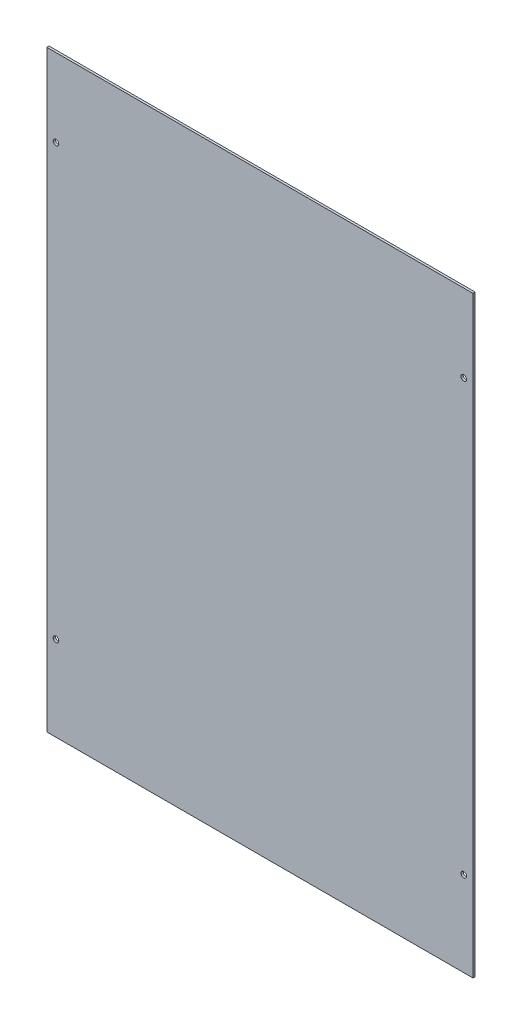
SolidWorks part; units mm, degrees
material "Acrylic (Medium-high impact)"
ref_plane "Front Plane" through (0, 0, 0) normal (0, 0, 1) x (1, 0, 0)
ref_plane "Top Plane" through (0, 0, 0) normal (0, 1, 0) x (1, 0, 0)
ref_plane "Right Plane" through (0, 0, 0) normal (1, 0, 0) x (0, 0, -1)
sketch "Sketch1" plane through (0, 0, 0) normal (0, 0, 1) x (1, 0, 0)
  line L1 (292.1, -406.4) -> (-292.1, -406.4)
  line L2 (292.1, -406.4) -> (292.1, 406.4)
  line L3 (292.1, 406.4) -> (-292.1, 406.4)
  line L4 (-292.1, -406.4) -> (-292.1, 406.4)
  line L5 (292.1, -406.4) -> (-292.1, 406.4) construction
  line L6 (292.1, 406.4) -> (-292.1, -406.4) construction
  point P0 (0, 0)
  dimension "D1" = 584.2
  dimension "D2" = 812.8
extrude "Boss-Extrude1" add sketch "Sketch1" along normal blind 3.0734
sketch "Sketch3" plane through (0, 0, 3.0734) normal (0, 0, 1) x (1, 0, 0)
  line L0 (292.1, -406.4) -> (292.1, 406.4) construction
  line L1 (292.1, 406.4) -> (-292.1, 406.4) construction
  line L2 (0, 449.0266) -> (0, -490.5745) construction
  line L3 (-292.1, -406.4) -> (292.1, -406.4) construction
  circle A0 centre (279.5016, 299.72) radius 3.81
  circle A1 centre (-279.5016, -290.0934) radius 3.81
  circle A2 centre (279.5016, -290.0934) radius 3.81
  circle A3 centre (-279.5016, 299.72) radius 3.81
  dimension "D1" = 7.62
  dimension "D2" = 12.5984
  dimension "D3" = 106.68
  dimension "D4" = 116.3066
extrude "Cut-Extrude1" cut sketch "Sketch3" against normal through all
sketch "Sketch4" plane through (0, 0, 0) normal (0, 0, -1) x (-1, 0, 0)
  line L0 (-292.1, -393.7) -> (292.1, -393.7) construction
  line L1 (-292.1, -406.4) -> (-292.1, 406.4) construction
  line L2 (292.1, 406.4) -> (292.1, -406.4) construction
  line L3 (292.1, -406.4) -> (-292.1, -406.4) construction
  line L4 (0, 406.4) -> (0, -393.7) construction
  line L5 (-292.1, 406.4) -> (292.1, 406.4) construction
  line L6 (-0.508, -393.7) -> (0.508, -393.7)
  line L7 (0.508, -393.7) -> (0.508, -392.43)
  line L8 (0.508, -392.43) -> (1.016, -392.43)
  line L9 (1.016, -392.43) -> (0, -391.16)
  line L10 (-0.508, -393.7) -> (-0.508, -392.43)
  line L11 (-0.508, -392.43) -> (-1.016, -392.43)
  line L12 (-1.016, -392.43) -> (0, -391.16)
  dimension "D1" = 12.7
  dimension "D2" = 1.016
  dimension "D3" = 2.032
  dimension "D4" = 1.27
  dimension "D5" = 1.27
extrude "Cut-Extrude2" cut sketch "Sketch4" against normal blind 2.54
equation "\"Height\"= 32in"
equation "\"Width\"= 23in"
equation "\"Depth\"= 20in"
equation "\"Plexi\"= .121in"
equation "\"MagnetThickness\"= 0.125in"
equation "\"MagnetDiameter\"= 12mm"
equation "\"DoorPlexi\" = \"Plexi\""
equation "\"BasePlateThickness\" = 0.5in"
equation "\"BasePlateWidth\" = \"Width\"+\"EBWidth\"-2*\"Plexi\""
equation "\"BasePlateDepth\" = \"TopBarDepth\"+2*\"CornerCube\""
equation "\"Boxsize\" = .75in"
equation "\"Boxinner\" = .625in"
equation "\"CornerCube\" = 0.75in"
equation "\"FingerLength\" = 1.125in"
equation "\"FingerWidth\" = .625in"
equation "\"Cutwidth\"= .016in"
equation "\"Earsize\"= 1in + \"Cutwidth\" /2"
equation "\"Slotsize\" = 1in - \"CutWidth\" / 2"
equation "\"InnerWidth\" = \"Width\" - 2* \"Plexi\""
equation "\"InnerHeight\" = \"Height\" -2 * \"Plexi\""
equation "\"InnerDepth\" = \"Depth\" - 2*\"Plexi\""
equation "\"RearNumHoles\" = 4"
equation "\"RearHolesBorder\" = 2.25"
equation "\"RearHoleSpacing\" = (\"Width\" - 2*\"RearHolesBorder\") / (\"RearNumHoles\"-1)"
equation "\"RearBarLength\" = (\"InnerWidth\"-2*\"CornerCube\")"
equation "\"RearTopNumHoles\" = 4"
equation "\"RearTopHolesBorder\" = 3.1"
equation "\"RearTopHolesSpacing\" = (\"Width\" - 2*\"RearTopHolesBorder\") / (\"RearTopNumHoles\"-1)"
equation "\"SideTopNumHoles\" = 4"
equation "\"SideTopHoleOffset\"=\"CornerCube\"+\"FingerLength\"+\"Plexi\"+.5"
equation "\"SideTopHoleSpacing\" = (\"TopBarDepth\"-2*\"SideTopHoleOffset\") / (\"SideTopNumHoles\"-1)"
equation "\"SideHorizNumHoles\" = 4"
equation "\"SideHorizHoleBorder\" = 1.50"
equation "\"SideHorizHoleSpacing\" = (\"TopBarDepth\"-2*\"SideHorizHoleBorder\") / (\"SideHorizNumHoles\"-1)"
equation "\"SideVertBarLength\"=\"Height\"-\"BasePlateThickness\"-2*\"CornerCube\"-\"Plexi\""
equation "\"SideVertNumHoles\" = 4"
equation "\"SideVertHolesBorder\" = \"CornerCube\"+\"FingerLength\"+1.50"
equation "\"SideVertHoleSpacing\" = (\"SideVertBarLength\" - 2*(\"SideVertHolesBorder\"-\"Plexi\"-\"CornerCube\")) / (\"SideVertNumHoles\"-1)"
equation "\"RearSideVertNumHoles\" = 4"
equation "\"RearSideVertHolesBorder\" = 2.4"
equation "\"RearSideVertHoleSpacing\" = (\"SideVertBarLength\" - 2*(\"RearSideVertHolesBorder\"-\"Plexi\"-\"CornerCube\")) / (\"RearSideVertNumHoles\"-1)"
equation "\"RivetDia\" = .228in"
equation "\"SlotDepth\" = \"Plexi\" + 0.75in + .005in"
equation "\"SideSlotWidth\"   = \"Plexi\"+.005in"
equation "\"SidePanelVertSpacing\" = (\"Height\"-2*(1.75-\"Plexi\")) / 5"
equation "\"BottomPanelSideHoleSpacing\" = (\"InnerDepth\"-2*(1.75-\"Plexi\")) / 4"
equation "\"FrontDoorGap\" = .1in"
equation "\"TopDepth\" = \"Depth\"-\"DoorPlexi\"-\"FrontDoorGap\""
equation "\"TopBarDepth\" = \"Depth\"-\"DoorPlexi\"-\"Plexi\"-2*\"MagnetThickness\"-2*\"CornerCube\""
equation "\"D1@Sketch1\"=\"Width\""
equation "\"D2@Sketch1\"=\"Height\""
equation "\"D1@Boss-Extrude1\"=\"DoorPlexi\""
equation "\"EBWidth\" = 9in"
equation "\"ComponentMountDia\"=0.1770"
equation "\"ShelfThickness\" = .1250in"
equation "\"BoxsizeHalf\" = \"Boxsize\"/2"
equation "\"Rivet3_16Dia\" = .191in"
equation "\"BinderPostDia\" = .228in"
equation "\"CoolerDepth\" = 12in"
equation "\"ShelfGap\" = 0.5in"
equation "\"ShelfDepth\" = \"TopBarDepth\"+\"CornerCube\"-\"CoolerDepth\""
equation "\"ShelfBarDepth\"=\"ShelfDepth\"-2*\"CornerCube\""
equation "\"ShelfWidth\" = \"EBWidth\"-\"ShelfGap\""
equation "\"ShelfBarWidth\" = \"EBWidth\"-\"Boxsize\""
equation "\"ShelfBarWidthShort\" = \"ShelfBarWidth\"-\"Boxsize\"-\"ShelfGap\""
equation "\"ShelfHeight1\" = 13in"
equation "\"ShelfHeight2\" = 24in"
equation "\"IntakeWidth\"=4in"
equation "\"IntakeHeight\"=2in"
equation "\"ExhaustWidth\"=4in"
equation "\"ExhaustHeight\"=2in"
equation "\"VentSpacing\"=7in"
equation "\"VentVertLocation\"=12.75in"
equation "\"AngleBracketLengthShort\"=.625in"
equation "\"AngleBracketLengthLong\"=1in"
equation "\"AngleBracketWidth\"=.5in"
equation "\"AngleBracketThickness\"=.125in"
equation "\"AngleBracketHolePosShort\"=.358in"
equation "\"AngleBracketHolePosLong\"=.7in"
equation "\"AngleBracketHoleDia\"=\"Rivet3_16Dia\""
equation "\"ShelfBarAngleHole\"=\"ShelfGap\"+\"Boxsize\"+\"AngleBracketHolePosShort\""
equation "\"PSBracketThickness\" = .0641in"
equation "\"EBForwardMountOffset\" = 4.0in"
equation "\"EBForwardMount\" = 2*\"Boxsize\"+\"CoolerDepth\"+\"EBForwardMountOffset\""
equation "\"EBRearwardMountOffset\" = 1.5in"
equation "\"EBRearwardMount\"= \"Boxsize\"+\"EBRearwardMountOffset\""
equation "\"MagSealWidth\" = \"InnerWidth\""
equation "\"MagSealHeight\" = \"Height\"-\"BasePlateThickness\"-\"Plexi\""
equation "\"MagWidth\" = .500in"
equation "\"SiliconeSealOD\" = .3125in"
equation "\"SiliconeSealID\" = .1875in"
equation "\"SiliconeSealWidth\" = \"MagSealWidth\" - 2*\"MagWidth\"-\"SiliconeSealOD\""
equation "\"SiliconeSealHeigth\" = \"MagSealHeight\" - 2*\"MagWidth\"-\"SiliconeSealOD\""
equation "\"HooknLoopThick\" = .085in"
equation "\"HooknLoopWidth\" = 0.75in"
equation "\"HooknLoopHeigth\" = 0.75in"
equation "\"D2@Sketch3\"=\"Plexi\"+\"BoxsizeHalf\""
equation "\"D3@Sketch3\"=\"Plexi\"+\"Boxsize\"+3.329"
equation "\"D4@Sketch3\"=\"BasePlateThickness\"+\"Boxsize\"+3.329"
